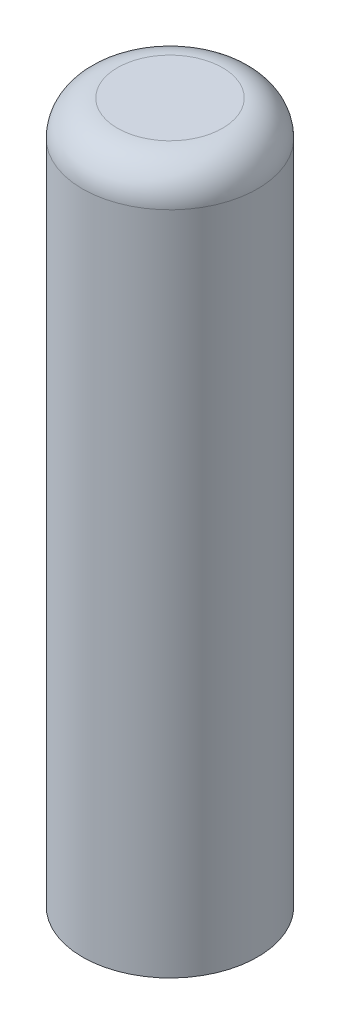
SolidWorks part; units mm, degrees
ref_plane "Front Plane" through (0, 0, 0) normal (0, 0, 1) x (1, 0, 0)
ref_plane "Top Plane" through (0, 0, 0) normal (0, 1, 0) x (1, 0, 0)
ref_plane "Right Plane" through (0, 0, 0) normal (1, 0, 0) x (0, 0, -1)
sketch "Sketch2" plane through (0, 0, 0) normal (0, 1, 0) x (1, 0, 0)
  line L1 (-0.975, 0.6) -> (0.975, 0.6)
  line L2 (-0.975, 0.6) -> (-0.975, -0.6)
  line L3 (-0.975, -0.6) -> (0.975, -0.6)
  line L4 (0.975, 0.6) -> (0.975, -0.6)
  line L5 (-0.975, 0.6) -> (0.975, -0.6) construction
  line L6 (-0.975, -0.6) -> (0.975, 0.6) construction
  circle A0 centre (0, 0) radius 2.5
  dimension "D1" = 5
  dimension "D2" = 1.2
  dimension "D3" = 1.95
extrude "Boss-Extrude1" add sketch "Sketch2" along normal mid plane 20
fillet "Fillet1" radius 1 1 edges at (0, 10, 2.5)
sketch "Sketch3" plane through (0, 10, 0) normal (0, 1, 0) x (1, 0, 0)
  line L0 (0.975, -0.6) -> (0.975, 0.6) construction
  line L1 (-0.975, -0.6) -> (0.975, -0.6) construction
  line L2 (-0.975, 0.6) -> (-0.975, -0.6) construction
  line L3 (0.975, 0.6) -> (-0.975, 0.6) construction
  line L4 (0.975, -0.6) -> (0.975, 0.6)
  line L5 (-0.975, -0.6) -> (0.975, -0.6)
  line L6 (-0.975, 0.6) -> (-0.975, -0.6)
  line L7 (0.975, 0.6) -> (-0.975, 0.6)
extrude "Boss-Extrude5" add sketch "Sketch3" against normal blind 16
